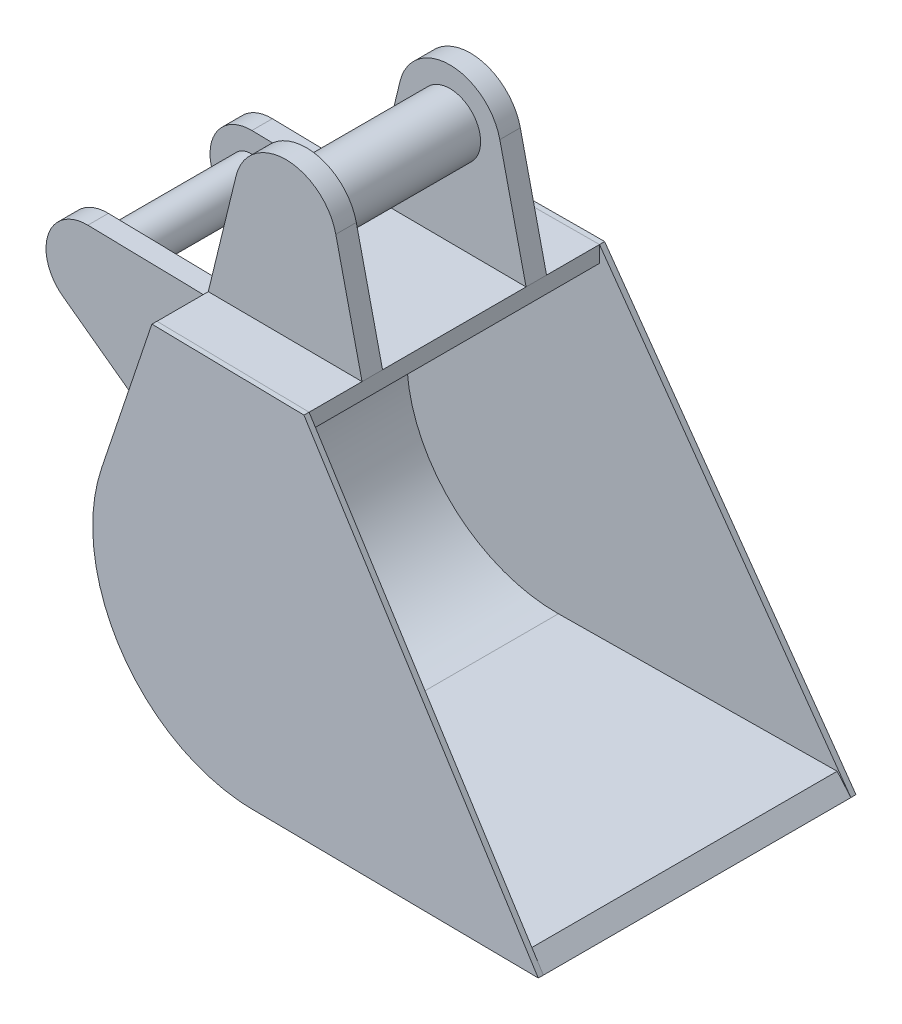
SolidWorks part; units mm, degrees
material "AISI 4340 Steel, normalized"
ref_plane "Front Plane" through (0, 0, 0) normal (0, 0, 1) x (1, 0, 0)
ref_plane "Top Plane" through (0, 0, 0) normal (0, 1, 0) x (1, 0, 0)
ref_plane "Right Plane" through (0, 0, 0) normal (1, 0, 0) x (0, 0, -1)
sketch "Sketch1" plane through (0, 0, 0) normal (0, 0, 1) x (1, 0, 0)
  line L0 (0, 0) -> (-269.0071, 0)
  line L1 (0, 0) -> (13, -16)
  line L2 (13, -16) -> (-269.0071, -16)
  line L3 (-405.8752, 188.7561) -> (-362.3296, 321.9224)
  line L4 (-362.3296, 321.9224) -> (-224.0127, 321)
  line L5 (-421.0828, 193.729) -> (-373.906, 338)
  line L6 (-373.906, 338) -> (-223.906, 336.9996)
  line L7 (-223.906, 336.9996) -> (-224.0127, 321)
  line L8 (-223.906, 336.9996) -> (13, -16) construction
  arc A0 (-405.8752, 188.7561) -> (-269.0071, 0) centre (-269.0071, 144) ccw
  arc A2 (-421.0828, 193.729) -> (-269.0071, -16) centre (-269.0071, 144) ccw
  point P6 (0, 0)
  point P9 (0, 0)
  point P14 (-270.2578, 139.7422)
  point P15 (-260.3675, 321)
  point P16 (0, 0)
  point P17 (0, 0)
  point P18 (-290.8198, 336.9982)
  dimension "D4" = 412
  dimension "D5" = 160
  dimension "D1" = 16
  dimension "D2" = 337
  dimension "D3" = 16
  dimension "D6" = 354
  dimension "D7" = 13
  dimension "D8" = 289
  dimension "D9" = 150
extrude "Boss-Extrude1" add sketch "Sketch1" along normal mid plane 300
ref_plane "Plane1" through (1.5596, 1.0467, 0) normal (0.8303, 0.5573, 0) x (0, 0, -1)
sketch "Sketch2" plane through (1.5596, 1.0467, 0) normal (0.8303, 0.5573, 0) x (0, 0, -1)
  line L0 (-150, -20.5298) -> (-140, 489.0169)
  line L1 (-150, 489.0169) -> (150, 489.0169) construction
  line L2 (0, 489.0169) -> (0, -20.5298) construction
  line L3 (-150, -20.5298) -> (150, -20.5298) construction
  line L4 (-140, 489.0169) -> (-150, 489.0169)
  line L5 (-150, 489.0169) -> (-150, -20.5298)
  line L6 (140, 489.0169) -> (150, 489.0169)
  line L7 (150, 489.0169) -> (150, -20.5298)
  line L8 (150, -20.5298) -> (140, 489.0169)
  dimension "D1" = 280
extrude "Cut-Extrude1" cut sketch "Sketch2" against normal through all
ref_plane "Plane2" through (-1.6354, 2.4368, 149.5395) normal (-0.0109, 0.0163, 0.9998) x (0.9999, 0.0001, 0.0109)
sketch "Sketch4" plane through (-1.6354, 2.4368, 149.5395) normal (-0.0109, 0.0163, 0.9998) x (0.9999, 0.0001, 0.0109)
  line L0 (14.6371, -18.4413) -> (-267.3869, -18.4034) construction
  line L1 (-419.4809, 191.3739) -> (-372.3075, 335.6577) construction
  line L2 (-372.3075, 335.6577) -> (-222.2985, 334.6371) construction
  line L3 (14.6371, -18.4413) -> (-267.3869, -18.4034)
  line L4 (-419.4809, 191.3739) -> (-372.3075, 335.6577)
  line L5 (-372.3075, 335.6577) -> (-222.2985, 334.6371)
  line L6 (-222.2985, 334.6371) -> (14.6371, -18.4413)
  ellipse E0 centre (-267.3939, 141.6179) end of major axis (-356.5665, 274.5017) minor radius 160 (-419.4809, 191.3739) -> (-267.3869, -18.4034) ccw construction
  ellipse E1 centre (-267.3939, 141.6179) end of major axis (-356.5665, 274.5017) minor radius 160 (-419.4809, 191.3739) -> (-267.3869, -18.4034) ccw
extrude "Boss-Extrude3" add sketch "Sketch4" along normal blind 5
sketch "Sketch5" plane through (0, 0, 0) normal (0, 0, 1) x (1, 0, 0)
  line L0 (-373.906, 338) -> (-223.906, 336.9996)
  line L1 (-373.906, 338) -> (-346.8218, 449.318)
  line L2 (-223.906, 336.9996) -> (-249.503, 448.669)
  line L4 (-421.0828, 193.729) -> (-515.8531, 263.1848)
  line L9 (-491.3775, 335.4393) -> (-373.906, 333)
  line L10 (-421.0828, 193.729) -> (-373.906, 333)
  arc A0 (-249.503, 448.669) -> (-346.8218, 449.318) centre (-298.2391, 437.4976) ccw
  circle A1 centre (-298.2391, 437.4976) radius 30 construction
  arc A2 (-491.3775, 335.4393) -> (-515.8531, 263.1848) centre (-492.2079, 295.4479) ccw
  circle A3 centre (-492.2079, 295.4479) radius 20 construction
  point P8 (-517.3268, 353.9801)
  point P15 (-516.2877, 303.6047)
  dimension "D2" = 60
  dimension "D3" = 20
  dimension "D4" = 40
  dimension "D5" = 20
  dimension "D1" = 100
  dimension "D6" = 5
  dimension "D7" = 100
extrude "Boss-Extrude4" add sketch "Sketch5" along normal blind 20 from offset 70
mirror "Mirror4" about plane through (0, 0, 0) normal (0, 0, 1) of "Boss-Extrude4", "Boss-Extrude3"
sketch "Sketch6" plane through (0, 0, 0) normal (0, 0, 1) x (1, 0, 0)
  circle A0 centre (-298.2391, 437.4976) radius 30 construction
  circle A1 centre (-492.2079, 295.4479) radius 20 construction
  circle A2 centre (-298.2391, 437.4976) radius 30
  circle A3 centre (-492.2079, 295.4479) radius 20
extrude "Boss-Extrude5" add sketch "Sketch6" along normal mid plane 180
